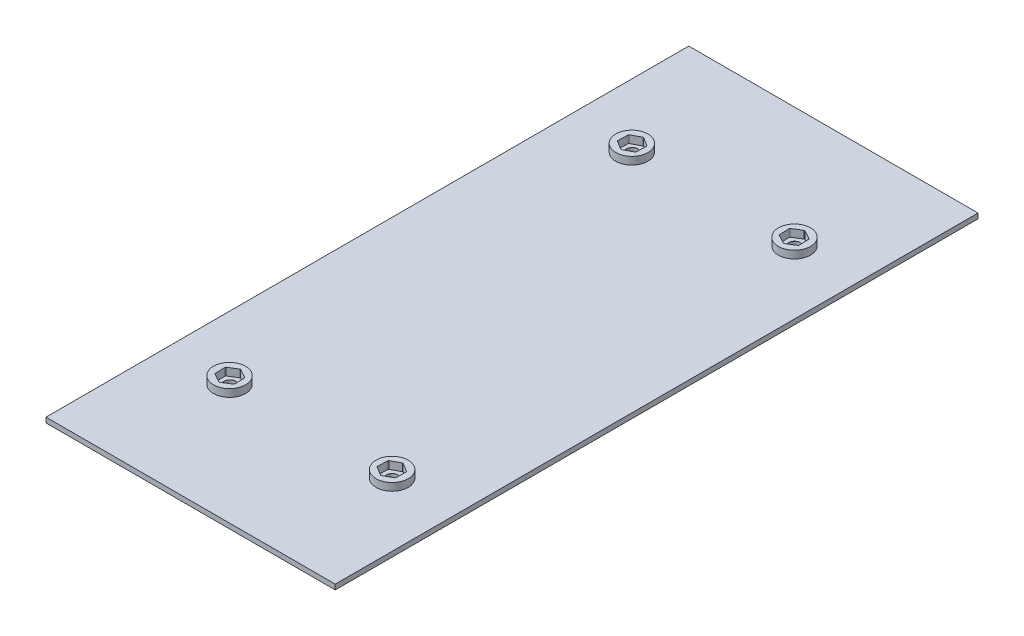
SolidWorks part; units mm, degrees
material "ABS"
ref_plane "Front Plane" through (0, 0, 0) normal (0, 0, 1) x (1, 0, 0)
ref_plane "Top Plane" through (0, 0, 0) normal (0, 1, 0) x (1, 0, 0)
ref_plane "Right Plane" through (0, 0, 0) normal (1, 0, 0) x (0, 0, -1)
sketch "Sketch1" plane through (0, 0, 0) normal (0, 1, 0) x (1, 0, 0)
  line L1 (0, 0) -> (114.3, 0)
  line L2 (0, 0) -> (0, 254)
  line L3 (0, 254) -> (114.3, 254)
  line L4 (114.3, 0) -> (114.3, 254)
  dimension "D1" = 254
  dimension "D2" = 114.3
extrude "Boss-Extrude1" add sketch "Sketch1" along normal blind 2
sketch "Sketch2" plane through (0, 2, 0) normal (0, 1, 0) x (1, 0, 0)
  line L0 (114.3, 254) -> (0, 254) construction
  line L2 (0, 254) -> (0, 0) construction
  point P0 (25.146, 206.502)
  point P1 (89.2773, 206.502)
  point P2 (89.2773, 47.5074)
  point P3 (25.146, 47.5074)
  point P6 (0, 0)
  point P9 (61.0148, 77.0554)
  point P10 (28.9075, 61.5963)
  point P11 (0, 0)
  point P12 (89.2773, 60.8216)
  point P13 (85.2239, 184.0637)
  point P14 (0, 0)
  dimension "D1" = 64.1313
  dimension "D2" = 158.9946
  dimension "D3" = 47.498
  dimension "D4" = 25.146
hole_wizard "M4 Clearance Hole1" positions "Sketch5" profile "Sketch6" hole size "M4" standard "ANSI Metric" end condition through all
sketch "Sketch5" plane through (0, 2, 0) normal (0, 1, 0) x (1, 0, 0)
  point P0 (25.146, 206.502)
  point P3 (89.2773, 206.502)
  point P6 (89.2773, 47.5074)
  point P9 (25.146, 47.5074)
sketch "Sketch6" plane through (25.146, 2, -206.502) normal (1, 0, 0) x (0, 0, 1)
  line L0 (0, 0) -> (0, 2)
  line L1 (0, 2) -> (2.25, 2)
  line L2 (2.25, 2) -> (2.25, 0.025)
  line L3 (2.25, 0.025) -> (2.275, 0)
  line L5 (2.275, 0) -> (0, 0)
  line L6 (-2.25, 0.025) -> (-2.275, 0) construction
  line L11 (0, -6.35) -> (0, 107.95) construction
  dimension "Thru Hole Dia." = 4.5
  dimension "Thru Hole Depth" = 2
  dimension "Near C'Sink Dia." = 4.55
  dimension "Near C'Sink Angle" = 90
sketch "Sketch8" plane through (0, 2, 0) normal (0, 1, 0) x (1, 0, 0)
  line L0 (26.9954, 44.5359) -> (28.6252, 45.5503) construction
  line L1 (28.7076, 45.7047) -> (28.6441, 47.6233) construction
  line L2 (28.6441, 47.6233) -> (28.5805, 49.5419) construction
  line L3 (28.4881, 49.6905) -> (26.7947, 50.5948) construction
  line L4 (26.7947, 50.5948) -> (25.1013, 51.4991) construction
  line L5 (24.9264, 51.4933) -> (23.2966, 50.4789) construction
  line L6 (23.2966, 50.4789) -> (21.6668, 49.4645) construction
  line L7 (21.5844, 49.3102) -> (21.6479, 47.3915) construction
  line L8 (21.6479, 47.3915) -> (21.7115, 45.4729) construction
  line L9 (21.8039, 45.3243) -> (23.4973, 44.42) construction
  line L10 (23.4973, 44.42) -> (25.1907, 43.5158) construction
  line L11 (25.3656, 43.5216) -> (26.9954, 44.5359) construction
  line L12 (26.9954, 44.5359) -> (28.6252, 45.5503)
  line L13 (28.7076, 45.7047) -> (28.6441, 47.6233)
  line L14 (28.6441, 47.6233) -> (28.5805, 49.5419)
  line L15 (28.4881, 49.6905) -> (26.7947, 50.5948)
  line L16 (26.7947, 50.5948) -> (25.1013, 51.4991)
  line L17 (24.9264, 51.4933) -> (23.2966, 50.4789)
  line L18 (23.2966, 50.4789) -> (21.6668, 49.4645)
  line L19 (21.5844, 49.3102) -> (21.6479, 47.3915)
  line L20 (21.6479, 47.3915) -> (21.7115, 45.4729)
  line L21 (21.8039, 45.3243) -> (23.4973, 44.42)
  line L22 (23.4973, 44.42) -> (25.1907, 43.5158)
  line L23 (25.3656, 43.5216) -> (26.9954, 44.5359)
  line L24 (27.1296, 44.3203) -> (28.7594, 45.3346)
  line L25 (28.9615, 45.7131) -> (28.8979, 47.6317)
  line L26 (28.8979, 47.6317) -> (28.8344, 49.5503)
  line L27 (28.6077, 49.9146) -> (26.9143, 50.8188)
  line L28 (26.9143, 50.8188) -> (25.221, 51.7231)
  line L29 (24.7922, 51.7089) -> (23.1624, 50.6945)
  line L30 (23.1624, 50.6945) -> (21.5326, 49.6802)
  line L31 (21.3305, 49.3018) -> (21.3941, 47.3831)
  line L32 (21.3941, 47.3831) -> (21.4576, 45.4645)
  line L33 (21.6843, 45.1003) -> (23.3777, 44.196)
  line L34 (23.3777, 44.196) -> (25.071, 43.2917)
  line L35 (25.4998, 43.3059) -> (27.1296, 44.3203)
  line L36 (57.15, 0) -> (57.15, 254) construction
  line L37 (0, 0) -> (114.3, 0) construction
  line L38 (114.3, 254) -> (0, 254) construction
  line L39 (0, 127) -> (114.3, 127) construction
  line L40 (0, 254) -> (0, 0) construction
  line L41 (114.3, 0) -> (114.3, 254) construction
  line L42 (88.8002, 43.3059) -> (87.1704, 44.3203)
  line L43 (90.9223, 44.196) -> (89.229, 43.2917)
  line L44 (92.6157, 45.1003) -> (90.9223, 44.196)
  line L45 (92.9059, 47.3831) -> (92.8424, 45.4645)
  line L46 (92.9695, 49.3018) -> (92.9059, 47.3831)
  line L47 (91.1376, 50.6945) -> (92.7674, 49.6802)
  line L48 (89.5078, 51.7089) -> (91.1376, 50.6945)
  line L49 (87.3857, 50.8188) -> (89.079, 51.7231)
  line L50 (85.6923, 49.9146) -> (87.3857, 50.8188)
  line L51 (85.4021, 47.6317) -> (85.4656, 49.5503)
  line L52 (85.3385, 45.7131) -> (85.4021, 47.6317)
  line L53 (87.1704, 44.3203) -> (85.5406, 45.3346)
  line L54 (90.9223, 209.804) -> (89.229, 210.7083)
  line L55 (92.6157, 208.8997) -> (90.9223, 209.804)
  line L56 (92.9059, 206.6169) -> (92.8424, 208.5355)
  line L57 (92.9695, 204.6982) -> (92.9059, 206.6169)
  line L58 (91.1376, 203.3055) -> (92.7674, 204.3198)
  line L59 (89.5078, 202.2911) -> (91.1376, 203.3055)
  line L60 (87.3857, 203.1812) -> (89.079, 202.2769)
  line L61 (85.6923, 204.0854) -> (87.3857, 203.1812)
  line L62 (85.4021, 206.3683) -> (85.4656, 204.4497)
  line L63 (85.3385, 208.2869) -> (85.4021, 206.3683)
  line L64 (87.1704, 209.6797) -> (85.5406, 208.6654)
  line L65 (88.8002, 210.6941) -> (87.1704, 209.6797)
  line L66 (25.4998, 210.6941) -> (27.1296, 209.6797)
  line L67 (23.3777, 209.804) -> (25.071, 210.7083)
  line L68 (21.6843, 208.8997) -> (23.3777, 209.804)
  line L69 (21.3941, 206.6169) -> (21.4576, 208.5355)
  line L70 (21.3305, 204.6982) -> (21.3941, 206.6169)
  line L71 (23.1624, 203.3055) -> (21.5326, 204.3198)
  line L72 (24.7922, 202.2911) -> (23.1624, 203.3055)
  line L73 (26.9143, 203.1812) -> (25.221, 202.2769)
  line L74 (28.6077, 204.0854) -> (26.9143, 203.1812)
  line L75 (28.8979, 206.3683) -> (28.8344, 204.4497)
  line L76 (28.9615, 208.2869) -> (28.8979, 206.3683)
  line L77 (27.1296, 209.6797) -> (28.7594, 208.6654)
  arc A0 (28.6252, 45.5503) -> (28.7076, 45.7047) centre (28.5327, 45.6989) ccw construction
  arc A2 (28.5805, 49.5419) -> (28.4881, 49.6905) centre (28.4056, 49.5361) ccw construction
  arc A4 (25.1013, 51.4991) -> (24.9264, 51.4933) centre (25.0189, 51.3447) ccw construction
  arc A6 (21.6668, 49.4645) -> (21.5844, 49.3102) centre (21.7593, 49.316) ccw construction
  arc A8 (21.7115, 45.4729) -> (21.8039, 45.3243) centre (21.8864, 45.4787) ccw construction
  arc A10 (25.1907, 43.5158) -> (25.3656, 43.5216) centre (25.2731, 43.6701) ccw construction
  arc A12 (28.6252, 45.5503) -> (28.7076, 45.7047) centre (28.5327, 45.6989) ccw
  arc A14 (28.5805, 49.5419) -> (28.4881, 49.6905) centre (28.4056, 49.5361) ccw
  arc A16 (25.1013, 51.4991) -> (24.9264, 51.4933) centre (25.0189, 51.3447) ccw
  arc A18 (21.6668, 49.4645) -> (21.5844, 49.3102) centre (21.7593, 49.316) ccw
  arc A20 (21.7115, 45.4729) -> (21.8039, 45.3243) centre (21.8864, 45.4787) ccw
  arc A22 (25.1907, 43.5158) -> (25.3656, 43.5216) centre (25.2731, 43.6701) ccw
  arc A24 (28.7594, 45.3346) -> (28.9615, 45.7131) centre (28.5327, 45.6989) ccw
  arc A25 (28.8344, 49.5503) -> (28.6077, 49.9146) centre (28.4056, 49.5361) ccw
  arc A26 (25.221, 51.7231) -> (24.7922, 51.7089) centre (25.0189, 51.3447) ccw
  arc A27 (21.5326, 49.6802) -> (21.3305, 49.3018) centre (21.7593, 49.316) ccw
  arc A28 (21.4576, 45.4645) -> (21.6843, 45.1003) centre (21.8864, 45.4787) ccw
  arc A29 (25.071, 43.2917) -> (25.4998, 43.3059) centre (25.2731, 43.6701) ccw
  circle A30 centre (89.2773, 47.5074) radius 6.35
  arc A31 (89.229, 43.2917) -> (88.8002, 43.3059) centre (89.0269, 43.6701) cw
  arc A32 (92.8424, 45.4645) -> (92.6157, 45.1003) centre (92.4136, 45.4787) cw
  arc A33 (92.7674, 49.6802) -> (92.9695, 49.3018) centre (92.5407, 49.316) cw
  arc A34 (89.079, 51.7231) -> (89.5078, 51.7089) centre (89.2811, 51.3447) cw
  arc A35 (85.4656, 49.5503) -> (85.6923, 49.9146) centre (85.8944, 49.5361) cw
  arc A36 (85.5406, 45.3346) -> (85.3385, 45.7131) centre (85.7673, 45.6989) cw
  circle A37 centre (25.0227, 47.5074) radius 6.35
  circle A38 centre (89.2773, 206.4926) radius 6.35
  arc A39 (89.229, 210.7083) -> (88.8002, 210.6941) centre (89.0269, 210.3299) ccw
  arc A40 (92.8424, 208.5355) -> (92.6157, 208.8997) centre (92.4136, 208.5213) ccw
  arc A41 (92.7674, 204.3198) -> (92.9695, 204.6982) centre (92.5407, 204.684) ccw
  arc A42 (89.079, 202.2769) -> (89.5078, 202.2911) centre (89.2811, 202.6553) ccw
  arc A43 (85.4656, 204.4497) -> (85.6923, 204.0854) centre (85.8944, 204.4639) ccw
  arc A44 (85.5406, 208.6654) -> (85.3385, 208.2869) centre (85.7673, 208.3011) ccw
  circle A45 centre (25.0227, 206.4926) radius 6.35
  arc A46 (25.071, 210.7083) -> (25.4998, 210.6941) centre (25.2731, 210.3299) cw
  arc A47 (21.4576, 208.5355) -> (21.6843, 208.8997) centre (21.8864, 208.5213) cw
  arc A48 (21.5326, 204.3198) -> (21.3305, 204.6982) centre (21.7593, 204.684) cw
  arc A49 (25.221, 202.2769) -> (24.7922, 202.2911) centre (25.0189, 202.6553) cw
  arc A50 (28.8344, 204.4497) -> (28.6077, 204.0854) centre (28.4056, 204.4639) cw
  arc A51 (28.7594, 208.6654) -> (28.9615, 208.2869) centre (28.5327, 208.3011) cw
  dimension "D2" = 12.7
  dimension "D1" = 0.254
extrude "Boss-Extrude3" add sketch "Sketch8" along normal blind 3 contours A45 L77 A51 L76 L75 A50 L74 L73 A49 L72 L71 A48 L70 L69 A47 L68 L67 A46 L66 | A38 A44 L64 L65 A39 L54 L55 A40 L56 L57 A41 L58 L59 A42 L60 L61 A43 L62 L63 | A37 | L27 L28 A26 L29 L30 A27 L31 L32 A28 L33 L34 A29 L35 L24 A24 L25 L26 A25 | A30 | L51 A35 L50 L49 A34 L48 L47 A33 L46 L45 A32 L44 L43 A31 L42 L53 A36 L52
